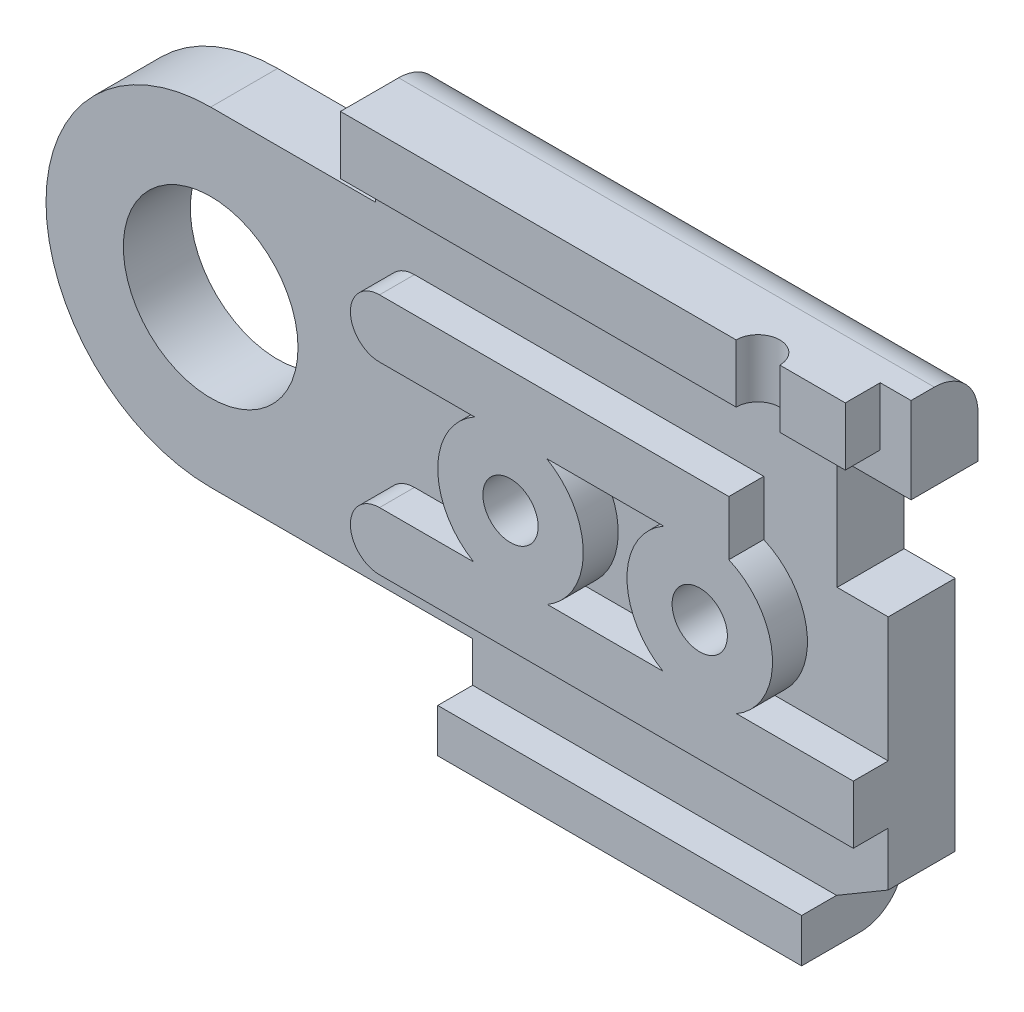
SolidWorks part; units mm, degrees
ref_plane "Front Plane" through (0, 0, 0) normal (0, 0, 1) x (1, 0, 0)
ref_plane "Top Plane" through (0, 0, 0) normal (0, 1, 0) x (1, 0, 0)
ref_plane "Right Plane" through (0, 0, 0) normal (1, 0, 0) x (0, 0, -1)
sketch "Sketch3" plane through (0, 0, 0) normal (0, 0, 1) x (1, 0, 0)
  line L7 (8, 0) -> (9, -2.5431)
  line L11 (30, 7) -> (27, 7.4569)
  line L13 (0, 7) -> (0, 7.5) construction
  line L14 (0, 7.5) -> (-22.3287, 7.5) construction
  line L15 (0, 5.3) -> (-14, 5.3) construction
  line L16 (0, 4) -> (-14, 4) construction
  line L17 (-14, 4) -> (-14, 5.3) construction
  line L18 (5.6569, 5.6569) -> (5.6569, 7.4569)
  line L19 (5.6569, 7.4569) -> (27, 7.4569)
  line L20 (21.5, -7.0431) -> (9, -7.0431)
  line L21 (9, -7.0431) -> (9, -2.5431)
  line L23 (25.0503, -4.9497) -> (21.5, -7.0431)
  arc A4 (8, 0) -> (5.6569, 5.6569) centre (0, 0) ccw
  arc A5 (25.0503, -4.9497) -> (30, 7) centre (30, 0) ccw
  circle A6 centre (0, 0) radius 7 construction
  circle A7 centre (0, 0) radius 3.9 construction
  circle A8 centre (0, 0) radius 5.3 construction
  circle A9 centre (0, 0) radius 4 construction
  dimension "D3" = 3.5503
  dimension "D17" = 14
  dimension "D4" = 14.5
  dimension "D5" = 135
  dimension "D2" = 5.6569
  dimension "D6" = 12.5
  dimension "D7" = 4.5
  dimension "D8" = 1
  dimension "D9" = 45
  dimension "D11" = 1.8
  dimension "D12" = 30
  dimension "D14" = 3
extrude "Boss-Extrude1" add sketch "Sketch3" along normal blind 2 contours A5 L11 L19 L18 A4 L7 L21 L20 L23
sketch "Sketch20" plane through (0, 0, 0) normal (0, 0, 1) x (1, 0, 0)
  line L0 (0, 7) -> (0, 7.5) construction
  line L1 (0, 7.5) -> (-19.4737, 7.5) construction
  line L2 (0, 5.3) -> (-14, 5.3) construction
  line L3 (0, 4) -> (-14, 4) construction
  line L4 (-14, 4) -> (-14, 5.3) construction
  line L5 (0, 5.3) -> (17.4849, 5.3) construction
  line L6 (17.4849, 5.3) -> (17.4849, 4) construction
  line L7 (17.4849, 4) -> (0, 4) construction
  line L8 (-2.5, 7.5) -> (-2.5, 2.868) construction
  circle A0 centre (0, 0) radius 7 construction
  circle A1 centre (0, 0) radius 3.9 construction
  circle A3 centre (0, 0) radius 5.3 construction
  circle A4 centre (0, 0) radius 4 construction
  circle A5 centre (0, 0) radius 2 construction
  dimension "D1" = 0
  dimension "D2" = 2.5
ref_plane "Plane1" through (0, 0, 2) normal (0, 0, 1) x (1, 0, 0)
sketch "Sketch4" plane through (0, 0, 2) normal (0, 0, 1) x (1, 0, 0)
  line L4 (5.6569, 5.6569) -> (5.6569, 7.5)
  line L5 (5.6569, 5.6569) -> (5.6569, 7.4569) construction
  line L6 (5.6569, 7.5) -> (21.5, 7.5)
  line L10 (8, 0) -> (9, -2.5431)
  line L11 (9, -2.5431) -> (9, -7.0431)
  line L12 (9, -7.0431) -> (21.5, -7.0431)
  line L13 (21.5, -7.0431) -> (21.5, 7.5)
  arc A0 (8, 0) -> (5.6569, 5.6569) centre (0, 0) ccw construction
  arc A3 (8, 0) -> (5.6569, 5.6569) centre (0, 0) ccw
sketch "Sketch22" plane through (0, 0, 2) normal (0, 0, 1) x (1, 0, 0)
  line L1 (5.6569, 7.4569) -> (21.5, 7.4569)
  line L6 (8, 0) -> (9, -2.5431)
  line L7 (9, -2.5431) -> (9, -7.0431)
  line L8 (9, -7.0431) -> (21.5, -7.0431)
  line L10 (21.5, 7.4569) -> (27, 7.4569)
  line L11 (27, 7.4569) -> (27, 2.1289)
  line L12 (27, 2.1289) -> (23.2751, 2.1289)
  line L13 (21.5, -7.0431) -> (23.2751, -5.9964)
  line L14 (25.0503, -4.9497) -> (21.5, -7.0431) construction
  line L15 (23.2751, -5.9964) -> (23.2751, 2.1289)
  line L16 (5.6569, 7.4569) -> (5.6569, 5.6569)
  arc A0 (8, 0) -> (5.6569, 5.6569) centre (0, 0) ccw
  dimension "D1" = 5.328
extrude "Boss-Extrude6" add sketch "Sketch22" along normal blind 4.5
sketch "Sketch25" plane through (0, 0, 2) normal (0, 0, 1) x (1, 0, 0)
  line L0 (0, 5.3) -> (18.0981, 5.3) construction
  line L1 (0, 4) -> (18.0981, 4) construction
  line L2 (18.0981, 4) -> (18.0981, 5.3) construction
sketch "Sketch26" plane through (0, 0, 2) normal (0, 0, 1) x (1, 0, 0)
  line L1 (18.0981, 5.3) -> (2.5301, 5.3)
  line L2 (18.0981, 4) -> (2.5301, 4)
  line L3 (2.5301, 5.3) -> (2.5301, 4)
  line L4 (18.0981, 5.3) -> (27, 5.3)
  line L5 (27, 2.1289) -> (27, 7.4569) construction
  line L6 (27, 5.3) -> (27, 4)
  line L7 (27, 4) -> (18.0981, 4)
extrude "Cut-Extrude6" cut sketch "Sketch26" along normal blind 4.5
ref_plane "Plane18" through (0, 0, 6.5) normal (0, 0, 1) x (1, 0, 0)
sketch "Sketch31" plane through (0, 0, 6.5) normal (0, 0, 1) x (1, 0, 0)
  line L0 (2.4327, 5.6569) -> (0, 5.6569)
  line L4 (9, -5.6569) -> (0, -5.6569)
  line L7 (2.4327, 5.6569) -> (5.6569, 5.6569)
  line L8 (5.6569, 5.6569) -> (5.6569, 7.4569)
  line L12 (9, -7.0431) -> (9, -5.6569)
  line L13 (9, -2.5431) -> (9, -7.0431) construction
  line L16 (27, 7.4569) -> (27, 2.1289)
  line L17 (27, 2.1289) -> (23.2751, 2.1289)
  line L18 (23.2751, -5.9964) -> (23.2751, 2.1289)
  line L21 (21.5, -7.0431) -> (23.2751, -5.9964)
  line L22 (5.6569, 7.4569) -> (5.6569, 8.9569)
  line L23 (5.6569, 8.9569) -> (27, 8.9569)
  line L24 (27, 8.9569) -> (27, 7.4569)
  line L25 (9, -7.0431) -> (9, -8.5431)
  line L26 (9, -8.5431) -> (21.5, -8.5431)
  line L27 (21.5, -8.5431) -> (21.5, -7.0431)
  line L28 (27, 7.4569) -> (5.6569, 7.4569) construction
  line L29 (9, -7.0431) -> (21.5, -7.0431) construction
  arc A0 (0, 5.6569) -> (0, -5.6569) centre (0, 0) ccw
  dimension "D1" = 5.6569
  dimension "D2" = 5.6569
  dimension "D3" = 1.5
  dimension "D4" = 1.5
extrude "Boss-Extrude14" add sketch "Sketch31" along normal blind 2.3 separate body
sketch "Sketch32" plane through (0, 0, 8.8) normal (0, 0, 1) x (1, 0, 0)
  circle A0 centre (0, 0) radius 3
  dimension "D1" = 6
extrude "Cut-Extrude7" cut sketch "Sketch32" against normal blind 2.3
sketch "Sketch33" plane through (0, 0, 8.8) normal (0, 0, 1) x (1, 0, 0)
  line L1 (5.6569, 8.9569) -> (5.6569, 6.9569)
  line L4 (9, -7.0431) -> (9, -8.5431)
  line L7 (7, -4.1569) -> (23.2751, -4.1569)
  line L11 (9, -8.5431) -> (21.5, -8.5431)
  line L15 (21.5, -8.5431) -> (21.5, -7.0431)
  line L16 (21.5, -7.0431) -> (9, -7.0431)
  line L17 (5.6569, 8.9569) -> (23, 8.9569)
  line L18 (27, 8.9569) -> (5.6569, 8.9569) construction
  line L21 (23, 6.9569) -> (23, 8.9569)
  line L22 (23.2751, -4.1569) -> (23.2751, -2.1569)
  line L23 (23.2751, -2.1569) -> (7, -2.1569)
  line L25 (23.2751, -5.9964) -> (23.2751, 2.1289) construction
  line L27 (5.6569, 6.9569) -> (23, 6.9569)
  line L28 (19, 2.172) -> (7, 2.172)
  line L30 (7, 4.172) -> (19, 4.172)
  line L33 (19, 2.172) -> (19, 4.172)
  line L34 (27, 2.1289) -> (27, 8.9569) construction
  line L35 (9, -8.5431) -> (21.5, -8.5431) construction
  arc A1 (7, -2.1569) -> (7, -4.1569) centre (7, -3.1569) ccw
  arc A2 (7, 4.172) -> (7, 2.172) centre (7, 3.172) ccw
  dimension "D2" = 2
  dimension "D3" = 2
  dimension "D4" = 0
  dimension "D5" = 2
  dimension "D6" = 4
  dimension "D8" = 4
extrude "Boss-Extrude15" add sketch "Sketch33" along normal blind 1.2
sketch "Sketch34" plane through (0, 0, 2) normal (0, 0, 1) x (1, 0, 0)
  line L0 (30, 5.3) -> (18.0981, 5.3) construction
  line L1 (30, 4) -> (18.0981, 4) construction
  circle A0 centre (30, 0) radius 2 construction
  circle A1 centre (30, 0) radius 5.3 construction
  circle A2 centre (30, 0) radius 4 construction
sketch "Sketch35" plane through (0, 0, 8.8) normal (0, 0, 1) x (1, 0, 0)
  line L0 (27, 2.1289) -> (27, 6)
  line L1 (27, 2.1289) -> (21.5204, 2.1289)
  line L2 (27, 6) -> (21.5204, 6)
  line L3 (21.5204, 2.1289) -> (21.5204, 6)
  line L4 (27, 2.1289) -> (27, 8.9569) construction
  dimension "D1" = 5.4796
extrude "Cut-Extrude8" cut sketch "Sketch35" against normal blind 2.4
sketch "Sketch36" plane through (0, 0, 6.4) normal (0, 0, 1) x (1, 0, 0)
  line L0 (27, 2.1289) -> (27, 4)
  line L1 (27, 2.1289) -> (23.3, 2.1289)
  line L2 (27, 4) -> (23.3, 4)
  line L3 (23.3, 2.1289) -> (23.3, 4)
  line L4 (21.5, -7.0431) -> (21.5, 7.5) construction
  dimension "D1" = 1.8
extrude "Cut-Extrude9" cut sketch "Sketch36" against normal blind 4.4
sketch "Sketch37" plane through (0, 0, 2) normal (0, 0, 1) x (1, 0, 0)
  circle A0 centre (30, 0) radius 3.9
  dimension "D1" = 7.8
extrude "Boss-Extrude16" add sketch "Sketch37" along normal blind 4.4
sketch "Sketch39" plane through (0, 0, 6.4) normal (0, 0, 1) x (1, 0, 0)
  line L0 (29, 0.9798) -> (29, -0.9798)
  arc A0 (29, -0.9798) -> (29, 0.9798) centre (30, 0) ccw
  dimension "D2" = 2.8
  dimension "D1" = 1
extrude "Cut-Extrude10" cut sketch "Sketch39" against normal through all
sketch "Sketch43" plane through (0, 0, 8.8) normal (0, 0, 1) x (1, 0, 0)
  line L2 (0, -5.6569) -> (9, -5.6569) construction
  circle A0 centre (11.5, 0) radius 2.5
  circle A1 centre (18, 0) radius 2.5
  dimension "D1" = 2.5
  dimension "D3" = 5
  dimension "D4" = 6.5
  dimension "D2" = 5.6569
extrude "Boss-Extrude17" add sketch "Sketch43" along normal blind 1.2
sketch "Sketch44" plane through (0, 0, 10) normal (0, 0, 1) x (1, 0, 0)
  circle A0 centre (11.5, 0) radius 0.95
  circle A1 centre (18, 0) radius 0.95
  dimension "D1" = 1.9
  dimension "D2" = 1.9
extrude "Cut-Extrude11" cut sketch "Sketch44" against normal through all
sketch "Sketch45" plane through (0, 0, 0) normal (0, 0, -1) x (-1, 0, 0)
  circle A0 centre (-11.5, 0) radius 2
  circle A1 centre (-18, 0) radius 2
extrude "Cut-Extrude12" cut sketch "Sketch45" against normal blind 4.5
ref_plane "Plane17" through (0, 0, 10) normal (0, 0, 1) x (1, 0, 0)
sketch "Sketch48" plane through (0, 0, 2) normal (0, 0, 1) x (1, 0, 0)
  circle A0 centre (30, 0) radius 6 construction
  dimension "D1" = 12
sketch "Sketch49" plane through (0, 6.9569, 0) normal (0, -1, 0) x (1, 0, 0)
  line L0 (5.6569, 10) -> (23, 10) construction
  line L1 (23, 10) -> (23, 8.8) construction
  circle A0 centre (20, 10) radius 0.75
  dimension "D1" = 3
sketch "Sketch50" plane through (0, 0, 10) normal (0, 0, 1) x (1, 0, 0)
  line L0 (20, 6.9569) -> (27.3935, -5.0795) construction
extrude "Cut-Extrude13" cut sketch "Sketch49" against normal blind 3
sketch "Sketch51" plane through (0, 0, 8.8) normal (0, 0, 1) x (1, 0, 0)
  line L0 (27, 8.9569) -> (24.0587, 8.9569)
  line L1 (27, 8.9569) -> (27, 4.9913)
  line L2 (24.0587, 8.9569) -> (24.0587, 4.9913)
  line L3 (27, 4.9913) -> (24.0587, 4.9913)
  line L5 (27, 8.9569) -> (23, 8.9569) construction
extrude "Cut-Extrude14" cut sketch "Sketch51" against normal blind 6.8
fillet "Fillet1" radius 1.5 2 edges at (14.8578, 8.9569, 6.5) (15.25, -8.5431, 6.5)
fillet "Fillet3" radius 1 6 edges at (23.2751, -5.9964, 4.25) (24.0587, 7.4569, 4.25) (9, -7.0431, 3.25) (5.6569, 7.4569, 3.25) (15.25, -7.0431, 0) (16.3284, 7.4569, 0)
split "Split1" trim tools "Plane18" bodies to split 141 139 resulting bodies 142 143
delete or keep bodies "Body-Delete/Keep 1" type delete bodies bodies 143
